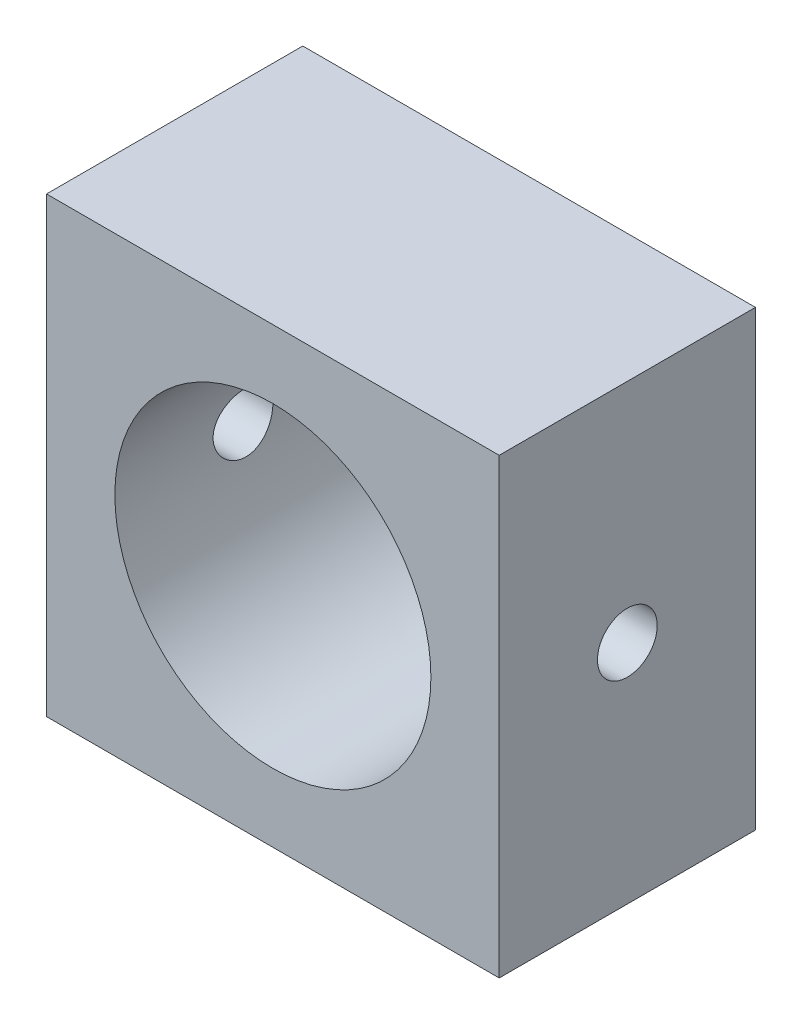
SolidWorks part; units mm, degrees
ref_plane "正面(Front)" through (0, 0, 0) normal (0, 0, 1) x (1, 0, 0)
ref_plane "平面(Top)" through (0, 0, 0) normal (0, 1, 0) x (1, 0, 0)
ref_plane "右側面(Right)" through (0, 0, 0) normal (1, 0, 0) x (0, 0, -1)
sketch "ｽｹｯﾁ1" plane through (0, 0, 0) normal (0, 0, 1) x (1, 0, 0)
  line L1 (10, 10) -> (-10, 10) construction
  line L2 (10, 10) -> (10, -10) construction
  line L3 (10, -10) -> (-10, -10) construction
  line L4 (-10, 10) -> (-10, -10) construction
  line L5 (10, 10) -> (-10, -10) construction
  line L6 (10, -10) -> (-10, 10) construction
  line L10 (-13.25, 13.25) -> (13.25, 13.25)
  line L13 (-13.25, 13.25) -> (-13.25, -13.25)
  line L14 (-13.25, -13.25) -> (13.25, -13.25)
  line L15 (13.25, 13.25) -> (13.25, -13.25)
  line L16 (-13.25, 13.25) -> (13.25, -13.25) construction
  line L17 (-13.25, -13.25) -> (13.25, 13.25) construction
  circle A0 centre (0, 0) radius 9.25
  dimension "D1" = 18.5
  dimension "D4" = 4
  dimension "D5" = 4
  dimension "D2" = 20
  dimension "D3" = 20
extrude "ﾎﾞｽ - 押し出し1" add sketch "ｽｹｯﾁ1" along normal mid plane 15
sketch "ｽｹｯﾁ3" plane through (0, 0, 0) normal (1, 0, 0) x (0, 0, -1)
  circle A0 centre (0, 0) radius 1.75
  dimension "D1" = 3.5
extrude "ｶｯﾄ - 押し出し1" cut sketch "ｽｹｯﾁ3" against normal through all both and the other way through all
